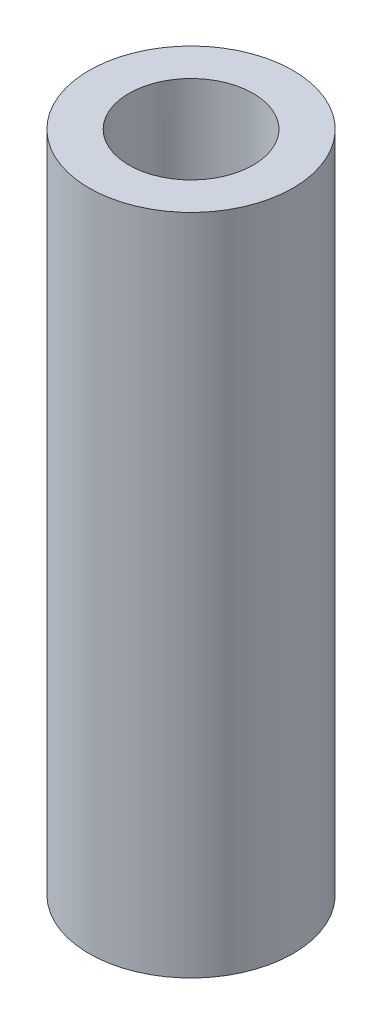
SolidWorks part; units mm, degrees
material "Silicon Rubber"
ref_plane "Front" through (0, 0, 0) normal (0, 0, 1) x (1, 0, 0)
ref_plane "Top" through (0, 0, 0) normal (0, 1, 0) x (1, 0, 0)
ref_plane "Right" through (0, 0, 0) normal (1, 0, 0) x (0, 0, -1)
sketch "Sketch1" plane through (0, 0, 0) normal (0, 0, 1) x (1, 0, 0)
  line L0 (0, 0) -> (0, 27.7812) construction
  line L1 (2.3813, 25.4) -> (2.3813, 0)
  line L2 (3.9052, 25.4) -> (3.9053, 0)
  line L3 (0, 29.3053) -> (0, 27.7812)
  line L4 (2.3813, 0) -> (3.9053, 0)
  arc A0 (0, 27.7812) -> (2.3813, 25.4) centre (0, 25.4) cw
  arc A1 (0, 29.3053) -> (3.9052, 25.4) centre (0, 25.4) cw
  dimension "Inside Height" = 25.4
  dimension "For OD" = 4.7625
  dimension "D1" = 1.524
revolve "Revolve1" add sketch "Sketch1" angle 360 about L0
sketch "Sketch2" plane through (0, 0, 0) normal (0, 0, 1) x (1, 0, 0)
  line L1 (-3.9053, 29.3052) -> (3.9053, 29.3053)
  line L2 (-3.9053, 29.3052) -> (-3.9053, 25.4)
  line L3 (-3.9053, 25.4) -> (3.9053, 25.4)
  line L4 (3.9053, 29.3053) -> (3.9053, 25.4)
  line L6 (-3.9053, 25.4) -> (3.9053, 25.4) construction
  arc A0 (3.9053, 25.4) -> (-3.9053, 25.4) centre (0, 25.4) ccw construction
  arc A1 (3.9053, 25.4) -> (-3.9053, 25.4) centre (0, 25.4) ccw construction
extrude "Cut-Extrude1" cut sketch "Sketch2" against normal through all both and the other way through all
